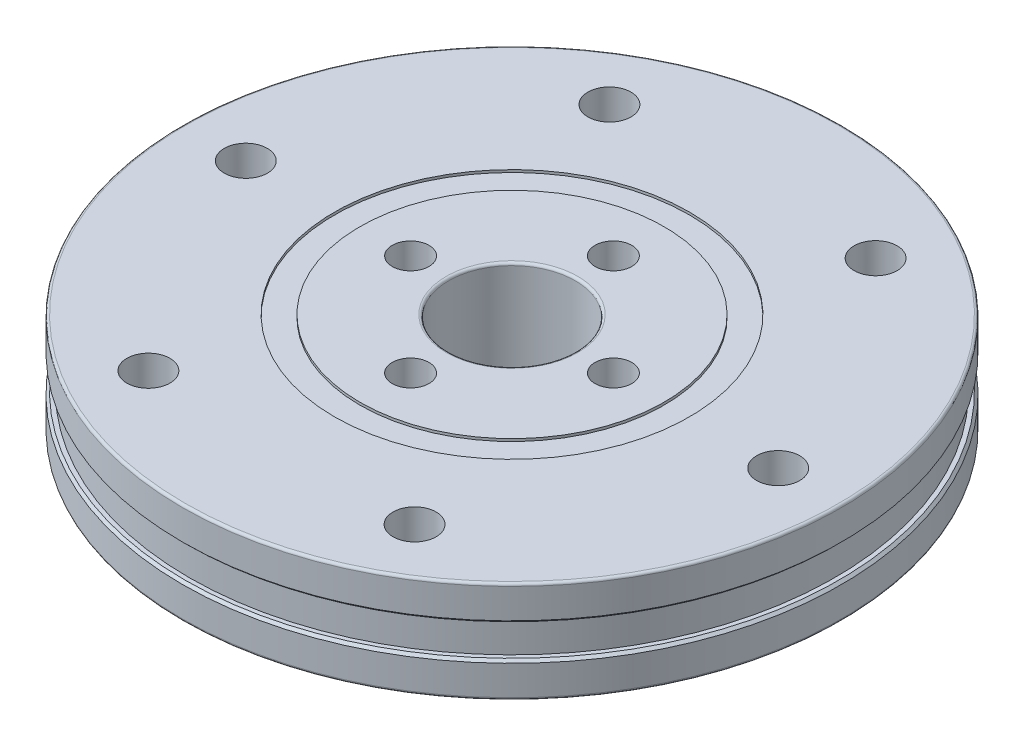
SolidWorks part; units mm, degrees
material "6061 合金"
ref_plane "前视基准面" through (0, 0, 0) normal (0, 0, 1) x (1, 0, 0)
ref_plane "上视基准面" through (0, 0, 0) normal (0, 1, 0) x (1, 0, 0)
ref_plane "右视基准面" through (0, 0, 0) normal (1, 0, 0) x (0, 0, -1)
sketch "草图1" plane through (0, 0, 0) normal (0, 1, 0) x (1, 0, 0)
  line L1 (-21, 0) -> (-10.5, -18.1865) construction
  line L2 (-10.5, -18.1865) -> (10.5, -18.1865) construction
  line L3 (10.5, -18.1865) -> (21, 0) construction
  line L4 (21, 0) -> (10.5, 18.1865) construction
  line L5 (10.5, 18.1865) -> (-10.5, 18.1865) construction
  line L6 (-10.5, 18.1865) -> (-21, 0) construction
  line L7 (0, -8) -> (8, 0) construction
  line L8 (8, 0) -> (0, 8) construction
  line L9 (0, 8) -> (-8, 0) construction
  line L10 (-8, 0) -> (0, -8) construction
  circle A0 centre (0, 0) radius 5
  circle A1 centre (0, 0) radius 26
  circle A3 centre (0, 0) radius 21 construction
  circle A4 centre (0, 0) radius 18.1865 construction
  circle A5 centre (-10.5, 18.1865) radius 1.7
  circle A6 centre (10.5, 18.1865) radius 1.7
  circle A7 centre (21, 0) radius 1.7
  circle A8 centre (10.5, -18.1865) radius 1.7
  circle A9 centre (-10.5, -18.1865) radius 1.7
  circle A10 centre (-21, 0) radius 1.7
  circle A11 centre (0, 0) radius 8 construction
  circle A12 centre (0, 0) radius 5.6569 construction
  circle A13 centre (0, 8) radius 1.45
  circle A14 centre (8, 0) radius 1.45
  circle A15 centre (0, -8) radius 1.45
  circle A16 centre (-8, 0) radius 1.45
  dimension "D1" = 10
  dimension "D2" = 52
  dimension "D3" = 42
  dimension "D4" = 3.4
  dimension "D5" = 16
  dimension "D6" = 2.9
extrude "凸台-拉伸1" add sketch "草图1" along normal mid plane 8
sketch "草图2" plane through (0, 4, 0) normal (0, 1, 0) x (1, 0, 0)
  circle A0 centre (0, 0) radius 12
  circle A1 centre (0, 0) radius 14
  dimension "D1" = 24
  dimension "D2" = 28
extrude "切除-拉伸1" cut sketch "草图2" against normal blind 0.2 contours A1 | A0
sketch "草图3" plane through (0, -4, 0) normal (0, -1, 0) x (1, 0, 0)
  circle A0 centre (0, 0) radius 12
  circle A1 centre (0, 0) radius 14
  dimension "D1" = 24
  dimension "D2" = 28
extrude "切除-拉伸2" cut sketch "草图3" against normal blind 0.2
sketch "草图5" plane through (0, 0, 0) normal (0, 1, 0) x (1, 0, 0)
  circle A0 centre (0, 0) radius 27.9239
  circle A1 centre (0, 0) radius 25.4684
extrude "切除-拉伸3" cut sketch "草图5" against normal mid plane 2.5
chamfer "倒角1" distance 0.2 angle 45 2 edges at (0, -1.25, 26) (0, 1.25, 26)
fillet "圆角1" radius 0.2 4 edges at (0, -4, 5) (0, -4, 26) (0, 4, 5) (0, 4, 26)
sketch "草图6" plane through (0, -4, 0) normal (0, -1, 0) x (1, 0, 0)
  circle A0 centre (-21, 0) radius 3.25
  circle A1 centre (-10.5, -18.1865) radius 3.25
  circle A2 centre (10.5, -18.1865) radius 3.25
  circle A3 centre (21, 0) radius 3.25
  circle A4 centre (10.5, 18.1865) radius 3.25
  circle A5 centre (-10.5, 18.1865) radius 3.25
  dimension "D1" = 6.5
extrude "切除-拉伸4" cut sketch "草图6" against normal blind 3.3
